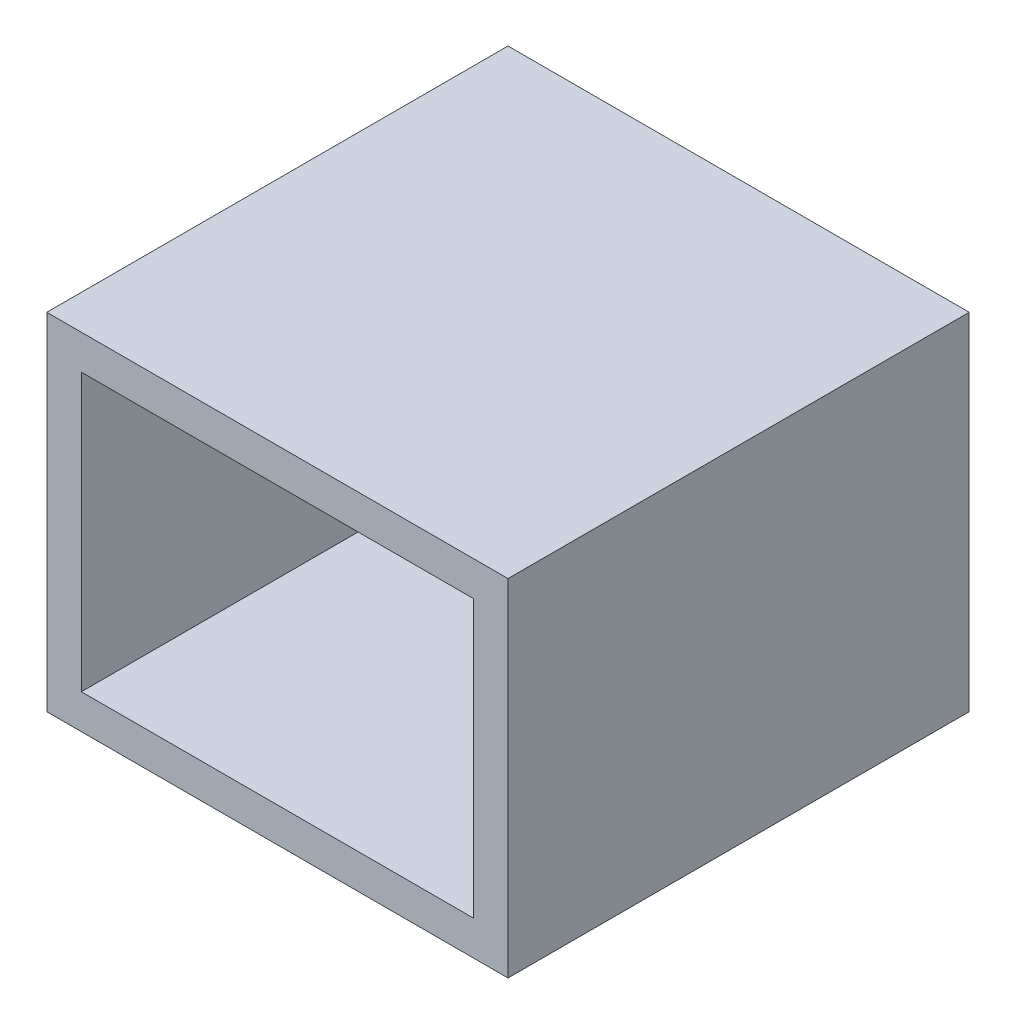
SolidWorks part; units mm, degrees
ref_plane "前视基准面" through (0, 0, 0) normal (0, 0, 1) x (1, 0, 0)
ref_plane "上视基准面" through (0, 0, 0) normal (0, 1, 0) x (1, 0, 0)
ref_plane "右视基准面" through (0, 0, 0) normal (1, 0, 0) x (0, 0, -1)
other "Configuration Table"
sketch "草图1" plane through (0, 0, 0) normal (0, 0, 1) x (1, 0, 0)
  line L1 (-13.6697, 31.3142) -> (26.3303, 31.3142)
  line L2 (-13.6697, 31.3142) -> (-13.6697, 1.3142)
  line L3 (-13.6697, 1.3142) -> (26.3303, 1.3142)
  line L4 (26.3303, 31.3142) -> (26.3303, 1.3142)
  dimension "D1" = 40
  dimension "D2" = 30
extrude "凸台-拉伸1" add sketch "草图1" along normal blind 40
sketch "草图2" plane through (0, 0, 40) normal (0, 0, 1) x (1, 0, 0)
  line L0 (-10.6697, 28.3142) -> (-10.6697, 4.3142)
  line L1 (-13.6697, 31.3142) -> (26.3303, 31.3142) construction
  line L2 (-13.6697, 31.3142) -> (-13.6697, 1.3142) construction
  line L3 (-13.6697, 1.3142) -> (26.3303, 1.3142) construction
  line L4 (26.3303, 31.3142) -> (26.3303, 1.3142) construction
  line L5 (-10.6697, 4.3142) -> (23.3303, 4.3142)
  line L6 (23.3303, 28.3142) -> (23.3303, 4.3142)
  line L7 (-10.6697, 28.3142) -> (23.3303, 28.3142)
  dimension "D1" = 3
extrude "切除-拉伸1" cut sketch "草图2" against normal blind 37
